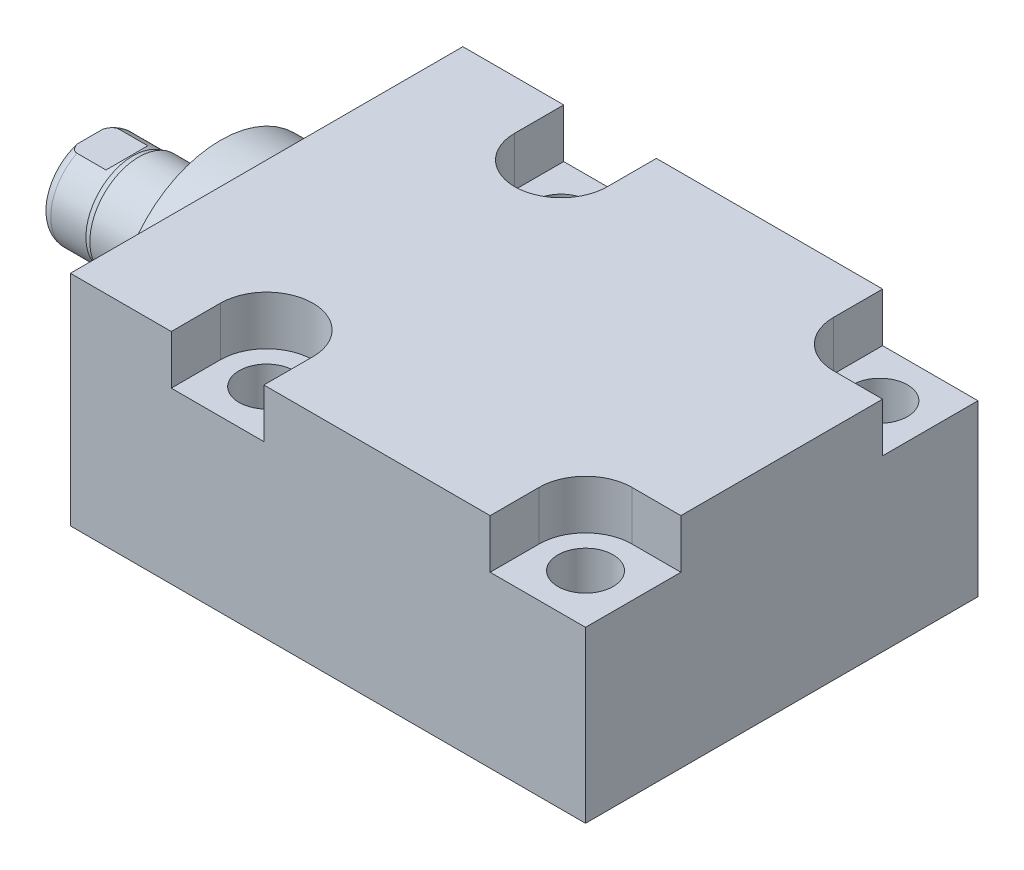
SolidWorks part; units mm, degrees
material "Alloy Steel"
ref_plane "Front Plane" through (0, 0, 0) normal (0, 0, 1) x (1, 0, 0)
ref_plane "Top Plane" through (0, 0, 0) normal (0, 1, 0) x (1, 0, 0)
ref_plane "Right Plane" through (0, 0, 0) normal (1, 0, 0) x (0, 0, -1)
ref_plane "Plane1" through (0, 0, 0) normal (1, 0, 0) x (0, 0, -1)
sketch "Sketch1" plane through (0, 0, 0) normal (1, 0, 0) x (0, 0, -1)
  line L0 (-25.4, 14.271) -> (25.4, 14.271)
  line L1 (25.4, 14.271) -> (25.4, -14.05)
  line L2 (25.4, -14.05) -> (-25.4, -14.05)
  line L3 (-25.4, -14.05) -> (-25.4, 14.271)
  line L4 (0, -24.4475) -> (0, 24.4475) construction
  dimension "D1" = 28.321
  dimension "D2" = 14.05
  dimension "D3" = 50.8
  dimension "D4" = 25.4
extrude "Extrude1" add sketch "Sketch1" along normal blind 66.675
sketch "Sketch5" plane through (0, 0, 0) normal (-1, 0, 0) x (0, 0, 1)
  circle A0 centre (0, 0) radius 13.5001
  dimension "D1" = 27.0002
extrude "Extrude2" add sketch "Sketch5" along normal blind 5.969
ref_plane "Plane5" through (0, 0, 0) normal (0, -1, 0) x (0, 0, 1)
sketch "Sketch6" plane through (0, 0, 0) normal (0, -1, 0) x (0, 0, 1)
  line L0 (0, 5.969) -> (-6.35, 5.969)
  line L1 (-6.35, 5.969) -> (-6.35, 22.86)
  line L2 (-6.35, 22.86) -> (0, 22.86)
  line L3 (0, 22.86) -> (0, 5.969)
  line L4 (0, -5.7546) -> (0, 21.1709) construction
  line L5 (13.5001, 5.969) -> (-13.5001, 5.969) construction
  line L6 (25.4, -66.675) -> (-25.4, -66.675) construction
  dimension "D1" = 89.535
  dimension "D2" = 12.7
revolve "Revolve1" add sketch "Sketch6" angle 360 about L4
ref_plane "Plane6" through (-18.5113, 3.2639, 0) normal (0, 0, 1) x (0, 1, 0)
sketch "S2D0001" plane through (-18.5113, 3.2639, 0) normal (0, 0, 1) x (0, 1, 0)
  line L0 (-0.7112, 2.7869) -> (-0.7112, -11.6533)
  line L1 (-3.2639, -13.1871) -> (-0.7112, -11.6533)
  line L2 (0.1905, 4.3487) -> (-3.2639, 4.3487)
  line L3 (-3.2639, 4.3487) -> (-3.2639, -13.1871)
  line L4 (-0.7112, 2.7869) -> (0.1905, 4.3487)
  line L5 (-3.2639, -18.5113) -> (-3.2639, 2.765) construction
  line L6 (3.0861, 4.3487) -> (-9.6139, 4.3487) construction
  dimension "D1" = 30
  dimension "D2" = 6.9088
  dimension "D3" = 5.1054
  dimension "D4" = 16.002
  dimension "D5" = 59
revolve "Cut-Revolve4" cut sketch "S2D0001" angle 360 about L5
ref_plane "Plane7" through (0, 0, 0) normal (0, 1, 0) x (0, 0, -1)
sketch "Sketch8" plane through (0, 0, 0) normal (0, 1, 0) x (0, 0, -1)
  line L0 (-6.35, 16.5354) -> (-6.096, 17.2974)
  line L1 (-6.096, 17.2974) -> (-6.096, 21.844)
  line L2 (0, 12.6594) -> (0, 20.8178) construction
  line L3 (-6.35, 16.5354) -> (-6.35, 22.86)
  line L4 (-5.7079, 22.86) -> (-6.35, 22.86)
  line L5 (6.35, 22.86) -> (-6.35, 22.86) construction
  line L6 (-6.35, 22.86) -> (-6.35, 5.969) construction
  arc A0 (-5.7079, 22.86) -> (-6.096, 21.844) centre (-4.572, 21.844) ccw
  dimension "D2" = 1.524
  dimension "D1" = 12.192
  dimension "D3" = 1.016
  dimension "D4" = 0.762
  dimension "D5" = 5.5626
revolve "Cut-Revolve5" cut sketch "Sketch8" angle 360 about L2
ref_plane "Plane11" through (0, 0, 0) normal (0, 0, -1) x (0, -1, 0)
sketch "Sketch12" plane through (0, 0, 0) normal (0, 0, -1) x (0, -1, 0)
  line L0 (5.461, 22.86) -> (5.461, 18.0848)
  line L1 (5.461, 18.0848) -> (6.096, 17.4498)
  line L2 (-5.461, 22.86) -> (-5.461, 18.0848)
  line L3 (-5.461, 18.0848) -> (-6.096, 17.4498)
  line L4 (5.461, 22.86) -> (6.096, 22.86)
  line L5 (0, 13.7262) -> (0, 20.767) construction
  line L6 (-6.096, 17.4498) -> (-6.096, 22.86)
  line L8 (6.096, 17.2974) -> (6.096, 21.844) construction
  line L9 (6.096, 17.4498) -> (6.096, 22.86)
  line L10 (-5.461, 22.86) -> (-6.096, 22.86)
  line L12 (5.7079, 22.86) -> (-5.7079, 22.86) construction
  dimension "D1" = 10.922
  dimension "D2" = 4.7752
  dimension "D3" = 45
extrude "Cut-Extrude4" cut sketch "Sketch12" against normal mid plane 60.96
hole_wizard "Hole2" positions "Sketch17" profile "Sketch16" legacy
sketch "Sketch17" plane through (0, 14.271, 0) normal (0, 1, 0) x (-1, 0, 0)
  line L0 (0, 0) -> (-59.3363, 0) construction
  line L1 (0, -25.4) -> (0, 25.4) construction
  point P0 (-19.05, -19.05)
  point P9 (-19.05, 19.05)
  dimension "D1" = 38.1
  dimension "D2" = 19.05
sketch "Sketch16" plane through (19.05, 14.271, -19.05) normal (1, 0, 0) x (0, 0, 1)
  line L0 (0, 0) -> (0, 28.321)
  line L1 (0, 28.321) -> (3.5687, 28.321)
  line L2 (3.5687, 28.321) -> (3.5687, 0)
  line L3 (3.5687, 0) -> (0, 0)
  line L4 (0, 110) -> (0, -10) construction
  dimension "Diameter" = 7.1374
  dimension "Depth" = 28.321
pattern_linear "LPattern1" count 2 spacing 41.275 along (1, 0, 0) of "Hole2"
sketch "Sketch18" plane through (0, 14.271, 0) normal (0, 1, 0) x (1, 0, 0)
  line L0 (0, 0) -> (50.053, 0) construction
  line L2 (66.675, -25.4) -> (0, -25.4) construction
  line L3 (66.675, 25.4) -> (66.675, -25.4) construction
  line L4 (66.675, -25.4) -> (54.3306, -25.4)
  line L5 (13.0556, -19.05) -> (13.0556, -25.4)
  line L6 (25.0444, -19.05) -> (25.0444, -25.4)
  line L7 (54.3306, -19.05) -> (54.3306, -25.4)
  line L8 (60.325, -13.0556) -> (66.675, -13.0556)
  line L9 (25.0444, -25.4) -> (13.0556, -25.4)
  line L10 (66.675, -13.0556) -> (66.675, -25.4)
  line L11 (66.675, 13.0556) -> (66.675, 25.4)
  line L12 (25.0444, 25.4) -> (13.0556, 25.4)
  line L13 (60.325, 13.0556) -> (66.675, 13.0556)
  line L14 (54.3306, 19.05) -> (54.3306, 25.4)
  line L15 (25.0444, 19.05) -> (25.0444, 25.4)
  line L16 (13.0556, 19.05) -> (13.0556, 25.4)
  line L17 (66.675, 25.4) -> (54.3306, 25.4)
  arc A0 (25.0444, -19.05) -> (13.0556, -19.05) centre (19.05, -19.05) ccw
  arc A1 (60.325, -13.0556) -> (54.3306, -19.05) centre (60.325, -19.05) ccw
  arc A2 (60.325, 13.0556) -> (54.3306, 19.05) centre (60.325, 19.05) cw
  arc A3 (25.0444, 19.05) -> (13.0556, 19.05) centre (19.05, 19.05) cw
  dimension "D1" = 11.9888
extrude "Cut-Extrude5" cut sketch "Sketch18" against normal blind 6.35
hole_wizard "Hole3" positions "Sketch20" profile "Sketch19" legacy
sketch "Sketch20" plane through (0, -14.05, 0) normal (0, -1, 0) x (1, 0, 0)
  line L0 (0, 25.4) -> (0, -25.4) construction
  point P0 (12.7, 0)
  dimension "D1" = 12.7
sketch "Sketch19" plane through (12.7, -14.05, 0) normal (1, 0, 0) x (0, 0, -1)
  line L0 (0, 0) -> (0, 14.9413)
  line L1 (0, 14.9413) -> (1.1938, 14.224)
  line L2 (1.1938, 14.224) -> (1.1938, 1.4478)
  line L3 (1.1938, 1.4478) -> (5.6705, 1.4478)
  line L4 (5.6705, 0) -> (0, 0)
  line L5 (0, -11.3109) -> (0, 121.1557) construction
  line L6 (0, 14.9413) -> (-1.1938, 14.224) construction
  line L7 (5.6705, 1.4478) -> (5.6705, 0)
  dimension "Depth" = 14.224
  dimension "Drill Angle" = 118
  dimension "Diameter" = 2.3876
  dimension "C-Bore Diameter" = 11.3411
  dimension "C-Bore Depth" = 1.4478
hole_wizard "Hole4" positions "Sketch21" profile "Sketch22" legacy
sketch "Sketch21" plane through (0, -14.05, 0) normal (0, -1, 0) x (1, 0, 0)
  point P0 (55.425, 0)
  dimension "D1" = 42.725
sketch "Sketch22" plane through (55.425, -14.05, 0) normal (1, 0, 0) x (0, 0, -1)
  line L0 (0, 0) -> (0, 15.1779)
  line L1 (0, 15.1779) -> (1.5875, 14.224)
  line L2 (1.5875, 14.224) -> (1.5875, 0)
  line L4 (1.5875, 0) -> (0, 0)
  line L5 (0, -11.3109) -> (0, 121.1557) construction
  line L6 (0, 15.1779) -> (-1.5875, 14.224) construction
  dimension "Depth" = 14.224
  dimension "Drill Angle" = 118
  dimension "Diameter" = 3.175
sketch "Sketch26" plane through (0, -14.05, 0) normal (0, -1, 0) x (1, 0, 0)
  circle A0 centre (53.975, 0) radius 5.6705
  dimension "D2" = 11.341
  dimension "D1" = 41.275
extrude "Cut-Extrude6" cut sketch "Sketch26" against normal blind 1.448
chamfer "Chamfer1" distance 0.635 angle 45 2 edges at (12.7, -12.6022, -1.1938) (55.425, -12.602, -1.5875)
sketch "Sketch23" plane through (0, 0, 0) normal (0, 0, 1) x (1, 0, 0)
  line L0 (12.7, -12.6022) -> (12.7, -21.4272) construction
  line L1 (10.8712, -12.6022) -> (14.5288, -12.6022) construction
  line L2 (7.0294, -12.6022) -> (18.3705, -12.6022) construction
  line L3 (7.0294, -12.6022) -> (7.0294, -14.05) construction
  circle A0 centre (8.4772, -14.05) radius 1.4478
  dimension "D1" = 2.8956
revolve "Revolve2" add sketch "Sketch23" angle 360 about L0
pattern_linear "LPattern3" count 2 spacing 41.275 along (1, 0, 0) of bodies 128
